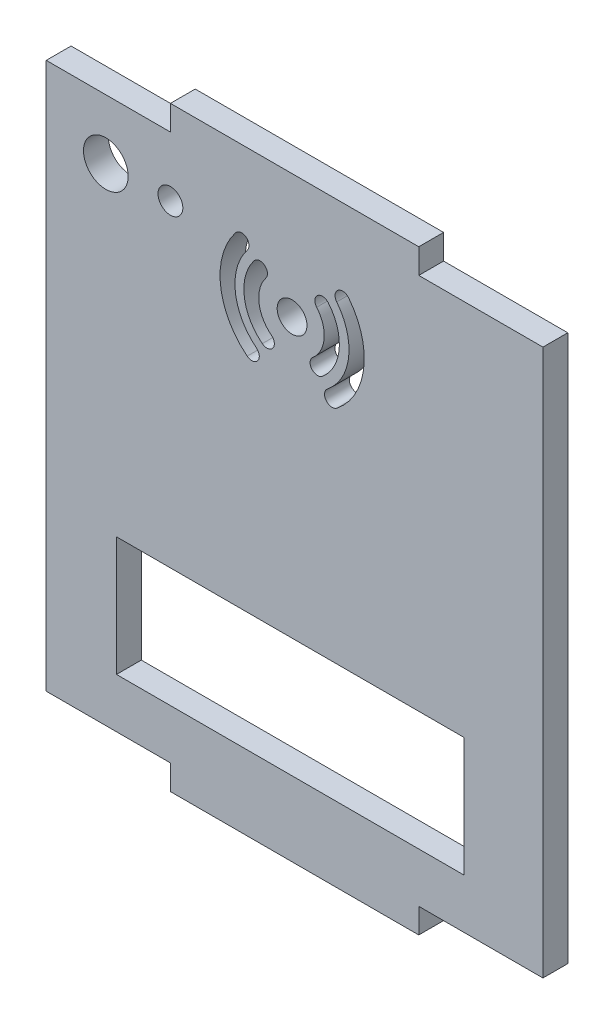
SolidWorks part; units mm, degrees
ref_plane "Front Plane" through (0, 0, 0) normal (0, 0, 1) x (1, 0, 0)
ref_plane "Top Plane" through (0, 0, 0) normal (0, 1, 0) x (1, 0, 0)
ref_plane "Right Plane" through (0, 0, 0) normal (1, 0, 0) x (0, 0, -1)
sketch "Sketch1" plane through (0, 0, 0) normal (0, 0, 1) x (1, 0, 0)
  line L0 (-63.2975, 0) -> (69.9162, 0) construction
  line L1 (-24.1439, 60) -> (25.8561, 60)
  line L2 (-49.1439, 55) -> (-49.1439, -55)
  line L3 (-24.1439, -60) -> (25.8561, -60)
  line L4 (50.8561, 55) -> (50.8561, -55)
  line L5 (25.8561, -55) -> (50.8561, -55)
  line L6 (25.8561, 55) -> (50.8561, 55)
  line L7 (-35, -21) -> (35, -21)
  line L8 (-49.1439, -55) -> (-24.1439, -55)
  line L9 (-49.1439, 55) -> (-24.1439, 55)
  line L10 (-24.1439, -60) -> (-24.1439, -55)
  line L11 (25.8561, 60) -> (25.8561, 55)
  line L12 (-24.1439, 55) -> (-24.1439, 60)
  line L14 (-35, -21) -> (-35, -45)
  line L15 (25.8561, -55) -> (25.8561, -60)
  line L21 (0, 3.1844) -> (0.3488, 3.0008) construction
  line L22 (0, 3.1844) -> (0.3488, 3.368) construction
  line L34 (0.3488, 3.368) -> (0.3488, 3.0008) construction
  line L35 (0, 3.1844) -> (0.3488, 3.1844) construction
  line L36 (0.3488, 3.0008) -> (0.3488, 3.368) construction
  line L37 (-35, -45) -> (35, -45)
  line L45 (35, -21) -> (35, -45)
  line L46 (-35, -21) -> (35, -45) construction
  line L47 (-35, -45) -> (35, -21) construction
  line L56 (0.3488, 32) -> (0.3488, 38) construction
  circle A2 centre (-37.1439, 43) radius 4.5
  circle A3 centre (0.3488, 35) radius 3
  arc A4 (6.4673, 40.1541) -> (5.5029, 28.8815) centre (0.3488, 35) cw construction
  arc A5 (6.484, 27.7169) -> (7.6319, 41.1352) centre (0.3488, 35) ccw
  arc A6 (4.5218, 30.0462) -> (5.3026, 39.173) centre (0.3488, 35) ccw
  arc A7 (4.5218, 30.0462) -> (6.484, 27.7169) centre (5.5029, 28.8815) ccw
  arc A8 (7.6319, 41.1352) -> (5.3026, 39.173) centre (6.4673, 40.1541) ccw
  arc A9 (-6.1092, 40.0647) -> (-4.7159, 28.542) centre (0.3488, 35) ccw construction
  arc A10 (-7.2895, 40.9904) -> (-5.6416, 27.3617) centre (0.3488, 35) ccw
  arc A11 (-4.9288, 39.1391) -> (-3.7902, 29.7223) centre (0.3488, 35) ccw
  arc A12 (-4.9288, 39.1391) -> (-7.2895, 40.9904) centre (-6.1092, 40.0647) ccw
  arc A13 (-5.6416, 27.3617) -> (-3.7902, 29.7223) centre (-4.7159, 28.542) ccw
  arc A14 (-9.8214, 43.0973) -> (-7.7485, 24.8298) centre (0.3488, 35) ccw construction
  arc A15 (-10.9949, 44.0316) -> (-8.6828, 23.6563) centre (0.3488, 35) ccw
  arc A16 (-8.6479, 42.163) -> (-6.8142, 26.0033) centre (0.3488, 35) ccw
  arc A17 (-8.6479, 42.163) -> (-10.9949, 44.0316) centre (-9.8214, 43.0973) ccw
  arc A18 (-8.6828, 23.6563) -> (-6.8142, 26.0033) centre (-7.7485, 24.8298) ccw
  arc A19 (10.5391, 43.0721) -> (8.4209, 24.8098) centre (0.3488, 35) cw construction
  arc A20 (9.3734, 23.6074) -> (11.7414, 44.0245) centre (0.3488, 35) ccw
  arc A21 (7.4685, 26.0121) -> (9.3367, 42.1197) centre (0.3488, 35) ccw
  arc A22 (7.4685, 26.0121) -> (9.3734, 23.6074) centre (8.4209, 24.8098) ccw
  arc A23 (11.7414, 44.0245) -> (9.3367, 42.1197) centre (10.5391, 43.0721) ccw
  circle A24 centre (-24.1439, 43) radius 2.5
  point P0 (0.3488, 3.1844)
  point P3 (0, -33)
  point P4 (0, 3.1844)
  point P42 (8.3197, 34.3181)
  point P53 (-7.799, 34.0148)
  point P61 (-12.5683, 33.5343)
  point P69 (13.2623, 33.5023)
  dimension "D11" = 9
  dimension "D12" = 12
  dimension "D1" = 5
  dimension "D2" = 110
  dimension "D3" = 50
  dimension "D7" = 100
  dimension "D9" = 70
  dimension "D10" = 10
  dimension "D13" = 12
  dimension "D14" = 24
  dimension "D17" = 25
extrude "Boss-Extrude1" add sketch "Sketch1" along normal blind 5
